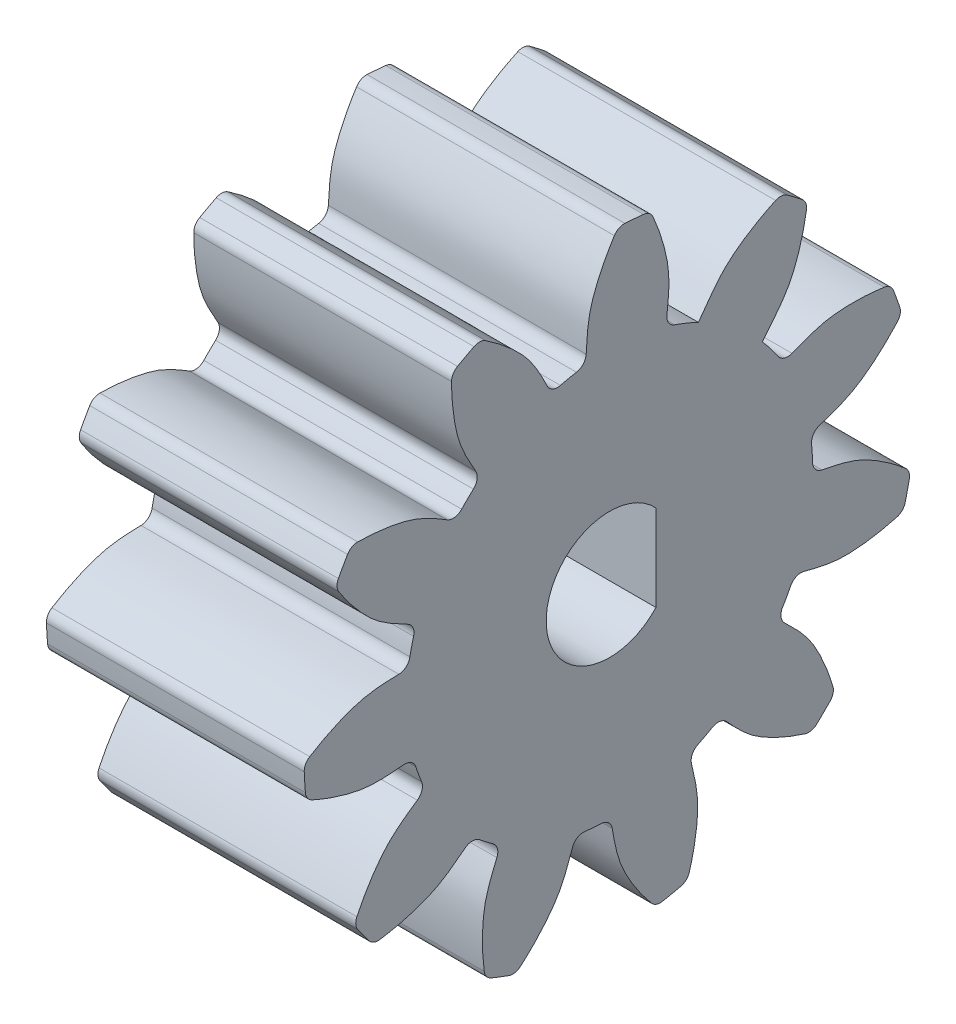
SolidWorks part; units mm, degrees
ref_plane "Front Plane" through (0, 0, 0) normal (0, 0, 1) x (1, 0, 0)
ref_plane "Top Plane" through (0, 0, 0) normal (0, 1, 0) x (1, 0, 0)
ref_plane "Right Plane" through (0, 0, 0) normal (1, 0, 0) x (0, 0, -1)
sketch "Sketch1" plane through (0, 0, 0) normal (1, 0, 0) x (0, 0, -1)
  circle A0 centre (0, 0) radius 8.7525
  dimension "D1" = 17.505
extrude "Boss-Extrude1" add sketch "Sketch1" along normal blind 11.1125
sketch "Sketch2" plane through (0, 0, 0) normal (-1, 0, 0) x (0, 0, 1)
  arc A0 (-0.3691, 13.1665) -> (-1.7539, 13.0541) centre (0.7161, -8.8065) ccw
  arc A1 (-2.4225, 8.4105) -> (1.0319, 8.6914) centre (0, 0) cw
  circle A2 centre (0, 0) radius 8.7525 construction
  spline S0 degree 3 poles (1.0319, 8.6914) (0.9852, 9.3803) (0.9836, 10.2515) (0.6576, 11.2193) (0.461, 11.7045) (0.1319, 12.374) (-0.1655, 12.8624) (-0.3691, 13.1665) knots 0 0 0 0 0.44087 0.531346 0.641017 0.769882 1 1 1 1
  spline S1 degree 3 poles (-2.4225, 8.4105) (-2.5012, 9.0996) (-2.6346, 9.9637) (-2.4637, 10.9737) (-2.3455, 11.4836) (-2.1253, 12.1954) (-1.9094, 12.7239) (-1.7539, 13.0541) knots 0 0 0 0 0.442214 0.532569 0.642094 0.770789 1 1 1 1
  point P2 (-0.3691, 13.1665)
  point P3 (-1.7539, 13.0541)
extrude "Boss-Extrude2" add sketch "Sketch2" against normal up to surface (11.1125 mm away) up to face at (11.1125, 0, -8.7525)
pattern_circular "CirPattern1" count 11 over 360 of "Boss-Extrude2"
fillet "Fillet1" radius 0.5004 42 edges at (5.5562, -3.5948, -7.9802) (5.5562, -4.9118, -7.2443) (5.5562, -7.3386, -4.7698) (5.5562, -8.0486, -3.4388) (5.5562, -8.7524, -0.0451) (5.5562, -8.6301, 1.4585) (5.5562, -7.3873, 4.6939) (5.5562, -6.4716, 5.8928) (5.5562, -3.6769, 7.9427) (5.5562, -2.2584, 8.4561) (5.5562, 1.2009, 8.6697) (5.5562, 2.6719, 8.3347) (5.5562, -0.2155, -8.7498) (5.5562, 5.6975, 6.6441) (5.5562, 6.7538, 5.5671) (5.5562, 8.3851, 2.5091) (5.5562, 8.6914, 1.0319) (5.5562, 8.4105, -2.4225) (5.5562, 4.5492, -7.4773) (5.5562, 1.2902, -8.6569) (5.5562, 7.0183, 11.1459) (5.5562, 5.8053, 11.8233) (5.5562, -0.1217, 13.1709) (5.5563, -1.5085, 13.085) (5.5562, -7.2231, 11.0143) (5.5563, -8.3433, 10.1922) (5.5562, -12.0312, 5.3607) (5.5562, -12.5292, 4.0635) (5.5562, -13.0195, -1.9949) (5.5562, -12.7371, -3.3553) (5.5562, -9.8742, -8.7171) (5.5563, -8.9011, -9.7089) (5.5562, -3.5939, -12.6717) (5.5562, -2.2391, -12.9799) (5.5562, 3.8274, -12.6031) (5.5562, 5.1338, -12.13) (5.5562, 10.0336, -8.5331) (5.5562, 10.8768, -7.4288) (5.5563, 11.2759, 6.8079) (5.5562, 11.9301, 5.5821) (5.5562, 13.1665, -0.3691) (5.5562, 13.0541, -1.7539)
sketch "Sketch3" plane through (0, 0, 0) normal (-1, 0, 0) x (0, 0, 1)
  line L0 (-2, 1.8589) -> (-2, -1.8589)
  circle A0 centre (0, 0) radius 2.7305 construction
  arc A1 (-2, 1.8589) -> (-2, -1.8589) centre (0, 0) cw
  dimension "D1" = 5.461
  dimension "D2" = 2
extrude "Cut-Extrude1" cut sketch "Sketch3" against normal through all contours A1 L0
